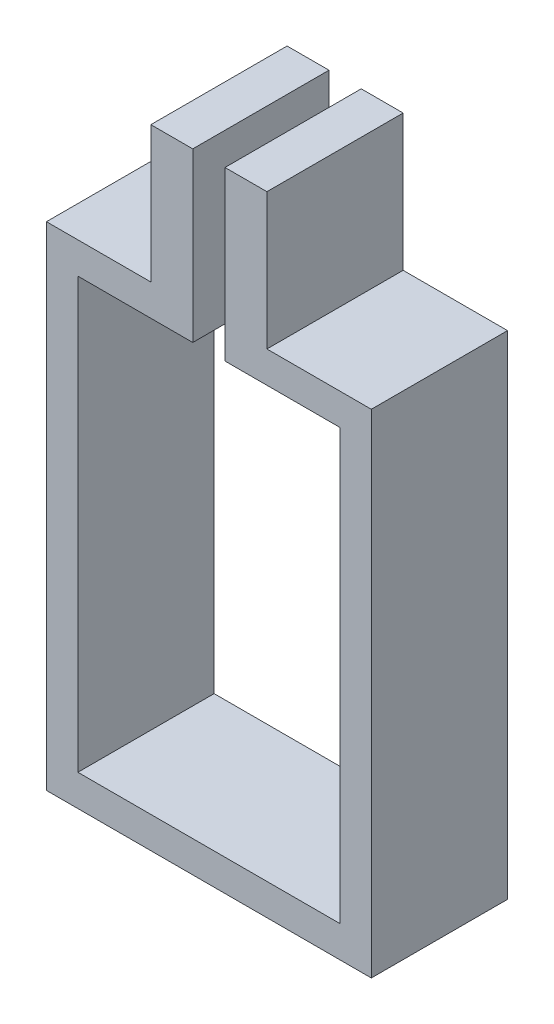
SolidWorks part; units mm, degrees
ref_plane "Alzado" through (0, 0, 0) normal (0, 0, 1) x (1, 0, 0)
ref_plane "Planta" through (0, 0, 0) normal (0, 1, 0) x (1, 0, 0)
ref_plane "Vista lateral" through (0, 0, 0) normal (1, 0, 0) x (0, 0, -1)
sketch "Croquis1" plane through (0, 0, 0) normal (0, 0, 1) x (1, 0, 0)
  line L1 (-15.5, 23.5) -> (15.5, 23.5)
  line L2 (-15.5, 23.5) -> (-15.5, -23.5)
  line L3 (-15.5, -23.5) -> (15.5, -23.5)
  line L4 (15.5, 23.5) -> (15.5, -23.5)
  line L5 (-15.5, 23.5) -> (15.5, -23.5) construction
  line L6 (-15.5, -23.5) -> (15.5, 23.5) construction
  point P1 (0, 0)
extrude "Saliente-Extruir1" add sketch "Croquis1" along normal blind 13
sketch "Croquis2" plane through (0, 0, 13) normal (0, 0, 1) x (1, 0, 0)
  line L1 (-12.5, 20.5) -> (12.5, 20.5)
  line L2 (-12.5, 20.5) -> (-12.5, -20.5)
  line L3 (-12.5, -20.5) -> (12.5, -20.5)
  line L4 (12.5, 20.5) -> (12.5, -20.5)
  line L5 (-12.5, 20.5) -> (12.5, -20.5) construction
  line L6 (-12.5, -20.5) -> (12.5, 20.5) construction
  point P0 (0, 0)
  dimension "D1" = 25
  dimension "D2" = 41
extrude "Cortar-Extruir1" cut sketch "Croquis2" against normal blind 13
sketch "Croquis3" plane through (0, 23.5, 0) normal (0, 1, 0) x (1, 0, 0)
  line L1 (-1.5377, 10.8542) -> (1.5377, 10.8542)
  line L2 (-1.5377, 10.8542) -> (-1.5377, -22.832)
  line L3 (-1.5377, -22.832) -> (1.5377, -22.832)
  line L4 (1.5377, 10.8542) -> (1.5377, -22.832)
  line L5 (-1.5377, 10.8542) -> (1.5377, -22.832) construction
  line L6 (-1.5377, -22.832) -> (1.5377, 10.8542) construction
  point P0 (0, -5.9889)
extrude "Cortar-Extruir2" cut sketch "Croquis3" against normal blind 13
sketch "Croquis4" plane through (0, 23.5, 0) normal (0, 1, 0) x (1, 0, 0)
  line L0 (15.5, 0) -> (1.5377, 0) construction
  line L1 (1.5377, -13) -> (5.5377, -13)
  line L2 (1.5377, -13) -> (1.5377, 0)
  line L3 (1.5377, 0) -> (5.5377, 0)
  line L4 (5.5377, -13) -> (5.5377, 0)
  line L5 (-1.5377, 0) -> (-15.5, 0) construction
  line L6 (-1.5377, -13) -> (-5.5377, -13)
  line L7 (-1.5377, -13) -> (-1.5377, 0)
  line L8 (-1.5377, 0) -> (-5.5377, 0)
  line L9 (-5.5377, -13) -> (-5.5377, 0)
  dimension "D1" = 4
  dimension "D2" = 4
extrude "Saliente-Extruir2" add sketch "Croquis4" along normal blind 13
